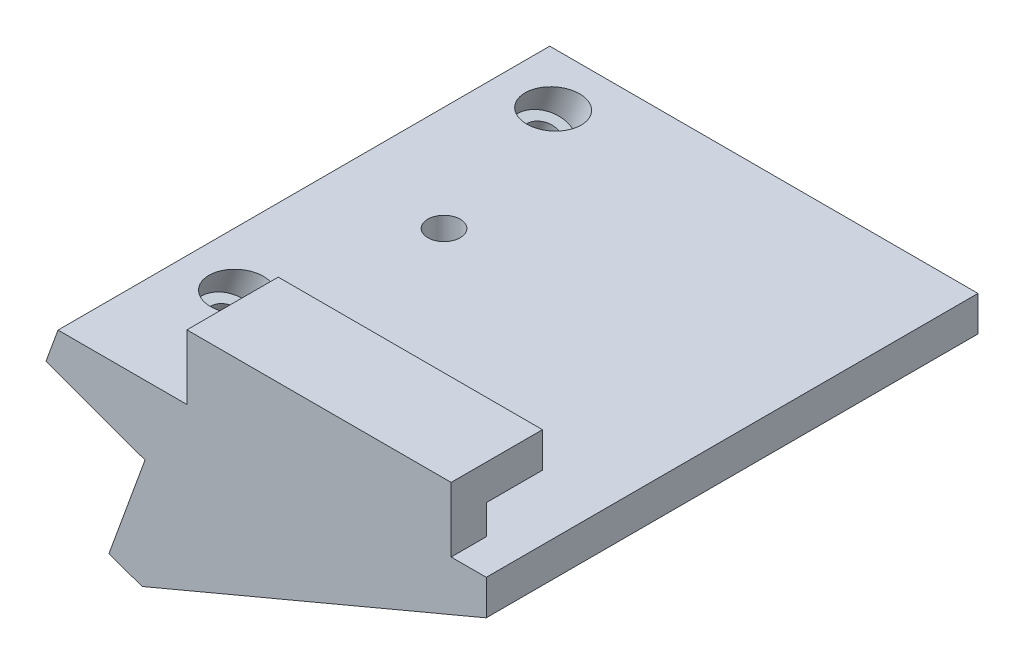
SolidWorks part; units mm, degrees
material "ABS"
ref_plane "正面" through (0, 0, 0) normal (0, 0, 1) x (1, 0, 0)
ref_plane "平面" through (0, 0, 0) normal (0, 1, 0) x (1, 0, 0)
ref_plane "右側面" through (0, 0, 0) normal (1, 0, 0) x (0, 0, -1)
sketch "ｽｹｯﾁ1" plane through (0, 0, 0) normal (0, 0, 1) x (1, 0, 0)
  line L6 (0, 0) -> (5.1303, 14.0954)
  line L7 (5.1303, 14.0954) -> (-8.9651, 19.2257)
  line L8 (-8.9651, 19.2257) -> (-7.255, 23.9242)
  line L9 (-7.255, 23.9242) -> (53.7077, 23.9242)
  line L10 (53.7077, 23.9242) -> (53.7077, 18.9242)
  line L11 (53.7077, 18.9242) -> (4.6985, -1.7101)
  line L12 (4.6985, -1.7101) -> (0, 0)
  line L13 (5.1303, 14.0954) -> (8.7077, 23.9242) construction
  dimension "D1" = 15
  dimension "D2" = 15
  dimension "D3" = 70
  dimension "D4" = 5
  dimension "D5" = 5
  dimension "D6" = 5
  dimension "0" = 45
extrude "ﾎﾞｽ - 押し出し1" add sketch "ｽｹｯﾁ1" along normal blind 65
sketch "ｽｹｯﾁ4" plane through (5.1303, 14.0954, 0) normal (-0.342, -0.9397, 0) x (-0.9397, 0.342, 0)
  line L0 (15, -65) -> (15, 0) construction
  line L1 (15, 0) -> (0, 0) construction
  line L2 (15, -65) -> (0, -65) construction
  circle A0 centre (7.5, -7.5) radius 2.25
  circle A1 centre (7.5, -52.5) radius 2.25
  dimension "D1" = 7.5
  dimension "D2" = 7.5
  dimension "D3" = 4.5
  dimension "D4" = 12.5
  dimension "D6" = 4.5
  dimension "D5" = 7.5
extrude "ｶｯﾄ - 押し出し2" cut sketch "ｽｹｯﾁ4" against normal blind 44
sketch "ｽｹｯﾁ5" plane through (5.1303, 14.0954, 0) normal (-0.342, -0.9397, 0) x (-0.9397, 0.342, 0)
  circle A0 centre (7.5, -52.5) radius 3.75
  circle A1 centre (7.5, -7.5) radius 3.75
  dimension "D1" = 7.5
  dimension "D2" = 7.5
extrude "ｶｯﾄ - 押し出し3" cut sketch "ｽｹｯﾁ5" against normal blind 44 from offset 3 offset against normal yes
sketch "ｽｹｯﾁ6" plane through (0, 0, 65) normal (0, 0, -1) x (-1, 0, 0)
  line L0 (-53.7077, 33.1242) -> (-53.7077, 18.9242)
  line L1 (-53.7077, 18.9242) -> (-4.6985, -1.7101)
  line L2 (-4.6985, -1.7101) -> (0, 0)
  line L3 (0, 0) -> (-5.1303, 14.0954)
  line L4 (-5.1303, 14.0954) -> (8.9651, 19.2257)
  line L5 (8.9651, 19.2257) -> (3.9065, 33.1242)
  line L6 (3.9065, 33.1242) -> (-53.7077, 33.1242)
  line L7 (-53.7077, 18.9242) -> (-53.7077, 23.9242) construction
  line L8 (-53.7077, 23.9242) -> (7.255, 23.9242) construction
  dimension "D1" = 9.2
extrude "ﾎﾞｽ - 押し出し2" add sketch "ｽｹｯﾁ6" against normal blind 5
sketch "ｽｹｯﾁ7" plane through (0, 0, 65) normal (0, 0, -1) x (-1, 0, 0)
  line L0 (3.9065, 33.1242) -> (5.7263, 28.1242)
  line L1 (7.255, 23.9242) -> (3.9065, 33.1242) construction
  line L2 (5.7263, 28.1242) -> (-53.7077, 28.1242)
  line L3 (-53.7077, 33.1242) -> (-53.7077, 23.9242) construction
  line L4 (-53.7077, 28.1242) -> (-53.7077, 33.1242)
  line L5 (-53.7077, 33.1242) -> (3.9065, 33.1242)
  dimension "D1" = 5
sketch "ｽｹｯﾁ8" plane through (0, 23.9242, 0) normal (0, 1, 0) x (1, 0, 0)
  line L0 (-7.255, 0) -> (-7.255, -65) construction
  line L2 (53.7077, 0) -> (-7.255, 0) construction
  circle A0 centre (7.695, -30) radius 2.3
  dimension "D1" = 14.95
  dimension "D3" = 4.6
  dimension "D2" = 30
extrude "ﾎﾞｽ - 押し出し3" add sketch "ｽｹｯﾁ7" along normal blind 8
extrude "ｶｯﾄ - 押し出し4" cut sketch "ｽｹｯﾁ8" against normal blind 3.5
sketch "ｽｹｯﾁ10" plane through (0, 0, 57) normal (0, 0, -1) x (-1, 0, 0)
  line L0 (7.255, 23.9242) -> (-11.0935, 23.9242)
  line L1 (-53.7077, 23.9242) -> (7.255, 23.9242) construction
  line L2 (-11.0935, 23.9242) -> (-11.0935, 33.1242)
  line L3 (3.9065, 33.1242) -> (-53.7077, 33.1242) construction
  line L4 (-11.0935, 33.1242) -> (3.9065, 33.1242)
  line L5 (3.9065, 33.1242) -> (7.255, 23.9242)
  dimension "D1" = 15
extrude "ｶｯﾄ - 押し出し6" cut sketch "ｽｹｯﾁ10" against normal through all
sketch "ｽｹｯﾁ11" plane through (53.7077, 0, 0) normal (1, 0, 0) x (0, 0, -1)
  line L0 (-65, 23.9242) -> (-70, 23.9242)
  line L1 (-70, 33.1242) -> (-70, 18.9242) construction
  line L2 (-70, 33.1242) -> (-57, 33.1242) construction
  line L3 (-57, 33.1242) -> (-57, 28.1242) construction
  line L4 (-57, 28.1242) -> (-65, 28.1242) construction
  line L5 (-65, 28.1242) -> (-65, 23.9242) construction
  line L6 (-70, 33.1242) -> (-70, 23.9242)
  line L7 (-70, 33.1242) -> (-57, 33.1242)
  line L8 (-57, 33.1242) -> (-57, 28.1242)
  line L9 (-57, 28.1242) -> (-65, 28.1242)
  line L10 (-65, 28.1242) -> (-65, 23.9242)
extrude "ｶｯﾄ - 押し出し7" cut sketch "ｽｹｯﾁ11" against normal blind 5
